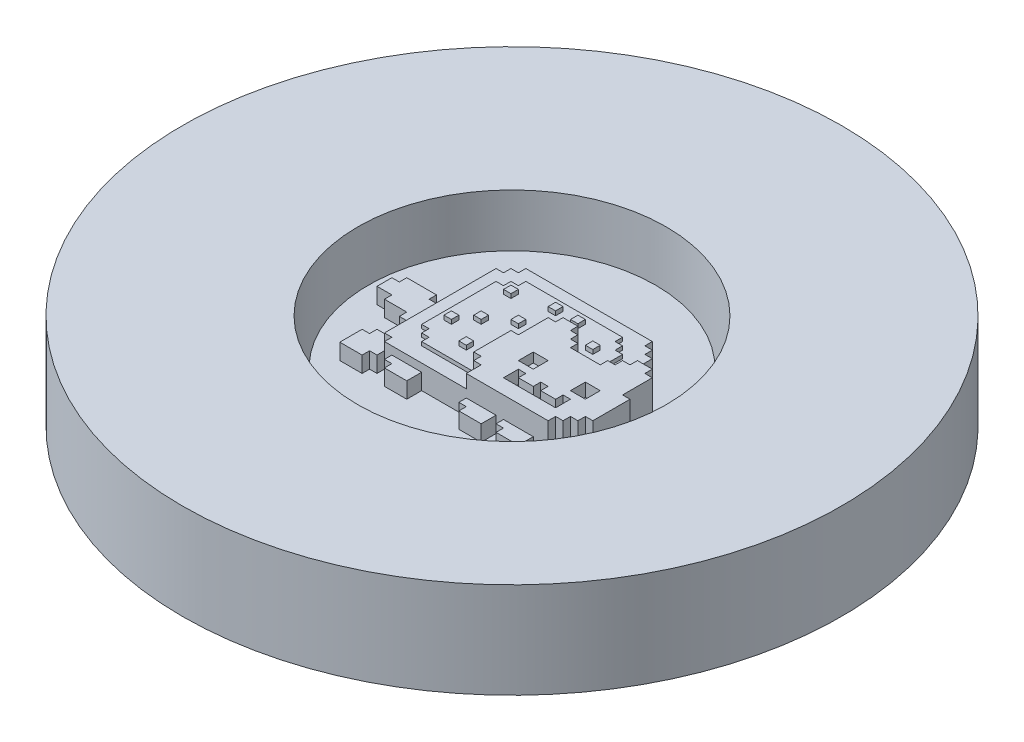
SolidWorks part; units mm, degrees
ref_plane "Front Plane" through (0, 0, 0) normal (0, 0, 1) x (1, 0, 0)
ref_plane "Top Plane" through (0, 0, 0) normal (0, 1, 0) x (1, 0, 0)
ref_plane "Right Plane" through (0, 0, 0) normal (1, 0, 0) x (0, 0, -1)
sketch "Sketch1"
sketch "face" plane through (0, 0, 0) normal (0, 1, 0) x (1, 0, 0)
  line L0 (103.124, 88.9) -> (110.236, 88.9)
  line L1 (110.236, 88.9) -> (110.236, 85.344)
  line L2 (110.236, 85.344) -> (113.792, 85.344)
  line L3 (113.792, 85.344) -> (113.792, 81.788)
  line L4 (113.792, 81.788) -> (117.348, 81.788)
  line L5 (117.348, 81.788) -> (117.348, 78.232)
  line L6 (117.348, 78.232) -> (131.572, 78.232)
  line L7 (131.572, 78.232) -> (131.572, 81.788)
  line L8 (131.572, 81.788) -> (135.128, 81.788)
  line L9 (135.128, 81.788) -> (135.128, 85.344)
  line L10 (135.128, 85.344) -> (138.684, 85.344)
  line L11 (138.684, 85.344) -> (138.684, 88.9)
  line L12 (138.684, 88.9) -> (145.796, 88.9)
  line L13 (145.796, 88.9) -> (145.796, 85.344)
  line L14 (145.796, 85.344) -> (149.352, 85.344)
  line L15 (149.352, 85.344) -> (149.352, 71.12)
  line L16 (149.352, 71.12) -> (152.908, 71.12)
  line L17 (152.908, 71.12) -> (152.908, 53.34)
  line L18 (152.908, 53.34) -> (149.352, 53.34)
  line L19 (149.352, 53.34) -> (149.352, 49.784)
  line L20 (149.352, 49.784) -> (145.796, 49.784)
  line L21 (145.796, 49.784) -> (145.796, 46.228)
  line L22 (145.796, 46.228) -> (142.24, 46.228)
  line L23 (142.24, 46.228) -> (142.24, 42.672)
  line L24 (142.24, 42.672) -> (103.124, 42.672)
  line L25 (103.124, 42.672) -> (103.124, 49.784)
  line L26 (103.124, 49.784) -> (99.568, 49.784)
  line L27 (99.568, 49.784) -> (99.568, 53.34)
  line L28 (99.568, 53.34) -> (96.012, 53.34)
  line L29 (96.012, 53.34) -> (96.012, 71.12)
  line L30 (96.012, 71.12) -> (99.568, 71.12)
  line L31 (99.568, 71.12) -> (99.568, 85.344)
  line L32 (99.568, 85.344) -> (103.124, 85.344)
  line L33 (110.236, 67.564) -> (110.236, 60.452)
  line L34 (110.236, 60.452) -> (117.348, 60.452)
  line L35 (117.348, 60.452) -> (117.348, 67.564)
  line L36 (117.348, 67.564) -> (110.236, 67.564)
  line L37 (135.128, 67.564) -> (135.128, 60.452)
  line L38 (135.128, 60.452) -> (142.24, 60.452)
  line L39 (142.24, 60.452) -> (142.24, 67.564)
  line L40 (142.24, 67.564) -> (135.128, 67.564)
  line L41 (113.792, 56.896) -> (113.792, 49.784)
  line L42 (113.792, 49.784) -> (138.684, 49.784)
  line L43 (138.684, 49.784) -> (138.684, 56.896)
  line L44 (138.684, 56.896) -> (135.128, 56.896)
  line L45 (135.128, 56.896) -> (135.128, 53.34)
  line L46 (135.128, 53.34) -> (128.016, 53.34)
  line L47 (128.016, 53.34) -> (128.016, 56.896)
  line L48 (128.016, 56.896) -> (124.46, 56.896)
  line L49 (124.46, 56.896) -> (124.46, 53.34)
  line L50 (124.46, 53.34) -> (117.348, 53.34)
  line L51 (117.348, 53.34) -> (117.348, 56.896)
  line L52 (117.348, 56.896) -> (113.792, 56.896)
  line L53 (103.124, 88.9) -> (103.124, 85.344)
sketch "poptart" plane through (0, 0, 0) normal (0, 1, 0) x (1, 0, 0)
  line L1 (135.128, 99.568) -> (131.572, 99.568)
  line L2 (131.572, 99.568) -> (131.572, 103.124)
  line L3 (131.572, 103.124) -> (128.016, 103.124)
  line L4 (128.016, 103.124) -> (128.016, 106.68)
  line L5 (128.016, 106.68) -> (67.564, 106.68)
  line L6 (67.564, 106.68) -> (67.564, 103.124)
  line L7 (67.564, 103.124) -> (64.008, 103.124)
  line L8 (64.008, 103.124) -> (64.008, 99.568)
  line L9 (64.008, 99.568) -> (60.452, 99.568)
  line L10 (60.452, 99.568) -> (60.452, 46.228)
  line L11 (60.452, 46.228) -> (64.008, 46.228)
  line L12 (64.008, 46.228) -> (64.008, 42.672)
  line L13 (64.008, 42.672) -> (135.128, 42.672)
  line L14 (142.24, 42.672) -> (103.124, 42.672) construction
  line L15 (135.128, 42.672) -> (145.796, 53.34)
  line L16 (145.796, 53.34) -> (145.796, 71.12)
  line L17 (145.796, 71.12) -> (135.128, 85.344)
  line L18 (135.128, 85.344) -> (135.128, 99.568)
sketch "feet tail" plane through (0, 0, 0) normal (0, 1, 0) x (1, 0, 0)
  line L0 (60.452, 74.676) -> (53.34, 74.676)
  line L1 (60.452, 99.568) -> (60.452, 46.228) construction
  line L2 (53.34, 74.676) -> (53.34, 78.232)
  line L3 (53.34, 78.232) -> (39.116, 78.232)
  line L4 (39.116, 78.232) -> (39.116, 74.676)
  line L5 (39.116, 74.676) -> (35.56, 74.676)
  line L6 (35.56, 74.676) -> (35.56, 67.564)
  line L7 (35.56, 67.564) -> (42.672, 67.564)
  line L8 (42.672, 67.564) -> (42.672, 64.008)
  line L9 (42.672, 64.008) -> (53.34, 64.008)
  line L10 (53.34, 64.008) -> (53.34, 60.452)
  line L11 (53.34, 60.452) -> (60.452, 60.452)
  line L12 (60.452, 60.452) -> (60.452, 74.676)
  line L13 (60.452, 53.34) -> (56.896, 53.34)
  line L14 (56.896, 53.34) -> (56.896, 49.784)
  line L15 (56.896, 49.784) -> (53.34, 49.784)
  line L16 (53.34, 49.784) -> (53.34, 46.228)
  line L17 (53.34, 46.228) -> (49.784, 46.228)
  line L18 (49.784, 46.228) -> (49.784, 35.56)
  line L19 (49.784, 35.56) -> (60.452, 35.56)
  line L20 (60.452, 35.56) -> (60.452, 39.116)
  line L21 (60.452, 39.116) -> (64.008, 39.116)
  line L22 (64.008, 39.116) -> (64.008, 46.228)
  line L23 (67.564, 42.672) -> (67.564, 39.116)
  line L24 (64.008, 42.672) -> (135.128, 42.672) construction
  line L25 (67.564, 39.116) -> (71.12, 39.116)
  line L26 (71.12, 39.116) -> (71.12, 35.56)
  line L27 (71.12, 35.56) -> (81.788, 35.56)
  line L28 (81.788, 35.56) -> (81.788, 42.672)
  line L29 (81.788, 42.672) -> (67.564, 42.672)
  line L30 (64.008, 46.228) -> (60.452, 46.228)
  line L31 (60.452, 46.228) -> (60.452, 53.34)
  line L33 (103.124, 42.672) -> (103.124, 39.116)
  line L34 (103.124, 39.116) -> (106.68, 39.116)
  line L35 (106.68, 39.116) -> (106.68, 35.56)
  line L36 (106.68, 35.56) -> (117.348, 35.56)
  line L37 (117.348, 35.56) -> (117.348, 42.672)
  line L38 (142.24, 42.672) -> (103.124, 42.672) construction
  line L39 (117.348, 42.672) -> (103.124, 42.672)
  line L40 (120.904, 42.672) -> (120.904, 39.116)
  line L41 (120.904, 39.116) -> (124.46, 39.116)
  line L42 (124.46, 39.116) -> (124.46, 35.56)
  line L43 (124.46, 35.56) -> (135.128, 35.56)
  line L44 (135.128, 35.56) -> (135.128, 42.672)
  line L45 (135.128, 42.672) -> (120.904, 42.672)
sketch "sprinkles" plane through (0, 0, 0) normal (0, 1, 0) x (1, 0, 0)
  line L1 (71.12, 67.564) -> (74.676, 67.564)
  line L2 (71.12, 67.564) -> (71.12, 64.008)
  line L3 (71.12, 64.008) -> (74.676, 64.008)
  line L4 (74.676, 67.564) -> (74.676, 64.008)
  line L5 (78.232, 74.676) -> (81.788, 74.676)
  line L6 (78.232, 74.676) -> (78.232, 71.12)
  line L7 (78.232, 71.12) -> (81.788, 71.12)
  line L8 (81.788, 74.676) -> (81.788, 71.12)
  line L9 (88.9, 81.788) -> (92.456, 81.788)
  line L10 (88.9, 81.788) -> (88.9, 78.232)
  line L11 (88.9, 78.232) -> (92.456, 78.232)
  line L12 (92.456, 81.788) -> (92.456, 78.232)
  line L13 (74.676, 92.456) -> (78.232, 92.456)
  line L14 (74.676, 92.456) -> (74.676, 88.9)
  line L15 (74.676, 88.9) -> (78.232, 88.9)
  line L16 (78.232, 92.456) -> (78.232, 88.9)
  line L17 (92.456, 96.012) -> (96.012, 96.012)
  line L18 (92.456, 96.012) -> (92.456, 92.456)
  line L19 (92.456, 92.456) -> (96.012, 92.456)
  line L20 (96.012, 96.012) -> (96.012, 92.456)
  line L21 (103.124, 96.012) -> (106.68, 96.012)
  line L22 (103.124, 96.012) -> (103.124, 92.456)
  line L23 (103.124, 92.456) -> (106.68, 92.456)
  line L24 (106.68, 96.012) -> (106.68, 92.456)
  line L25 (117.348, 88.9) -> (120.904, 88.9)
  line L26 (117.348, 88.9) -> (117.348, 85.344)
  line L27 (117.348, 85.344) -> (120.904, 85.344)
  line L28 (120.904, 88.9) -> (120.904, 85.344)
  line L29 (85.344, 60.452) -> (88.9, 60.452)
  line L30 (85.344, 60.452) -> (85.344, 56.896)
  line L31 (85.344, 56.896) -> (88.9, 56.896)
  line L32 (88.9, 60.452) -> (88.9, 56.896)
sketch "engrave poptart" plane through (0, 0, 0) normal (0, 1, 0) x (1, 0, 0)
  line L0 (71.12, 53.34) -> (74.676, 53.34)
  line L1 (74.676, 53.34) -> (74.676, 49.784)
  line L2 (74.676, 49.784) -> (99.8163, 49.76)
  line L3 (71.12, 53.34) -> (71.12, 56.896)
  line L4 (71.12, 56.896) -> (67.564, 56.896)
  line L5 (67.564, 56.896) -> (67.564, 92.456)
  line L6 (67.564, 92.456) -> (71.12, 92.456)
  line L7 (71.12, 92.456) -> (71.12, 96.012)
  line L8 (71.12, 96.012) -> (74.676, 96.012)
  line L9 (74.676, 96.012) -> (74.676, 99.568)
  line L10 (74.676, 99.568) -> (120.904, 99.568)
  line L11 (120.904, 99.568) -> (120.904, 96.012)
  line L12 (120.904, 96.012) -> (124.46, 96.012)
  line L13 (124.46, 96.012) -> (124.46, 92.456)
  line L14 (124.46, 92.456) -> (128.016, 92.456)
  line L15 (128.016, 92.456) -> (128.016, 67.564)
  line L16 (128.016, 67.564) -> (128.016, 64.008)
  line L17 (128.016, 64.008) -> (99.568, 49.784)
  line L18 (99.568, 49.784) -> (99.8163, 49.76)
sketch "rainbow tail" [suppressed] plane through (0, 0, 0) normal (0, 1, 0) x (1, 0, 0)
  line L0 (0, 39.116) -> (0, 49.784)
  line L1 (0, 49.784) -> (7.112, 49.784)
  line L2 (7.112, 49.784) -> (7.112, 53.34)
  line L3 (7.112, 53.34) -> (35.56, 53.34)
  line L4 (35.56, 53.34) -> (35.56, 49.784)
  line L5 (35.56, 49.784) -> (53.34, 49.784)
  line L6 (0, 39.116) -> (7.112, 39.116)
  line L7 (7.112, 39.116) -> (7.112, 42.672)
  line L8 (7.112, 42.672) -> (35.56, 42.672)
  line L9 (35.56, 42.672) -> (35.56, 39.116)
  line L10 (35.56, 39.116) -> (49.784, 39.116)
  line L11 (49.784, 46.228) -> (49.784, 35.56) construction
  line L12 (53.34, 49.784) -> (53.34, 46.228)
  line L13 (53.34, 46.228) -> (49.784, 46.228)
  line L14 (53.34, 60.452) -> (35.56, 60.452)
  line L15 (35.56, 60.452) -> (35.56, 64.008)
  line L16 (35.56, 64.008) -> (7.112, 64.008)
  line L17 (7.112, 64.008) -> (7.112, 60.452)
  line L18 (7.112, 60.452) -> (0, 60.452)
  line L19 (0, 60.452) -> (0, 71.12)
  line L20 (49.784, 46.228) -> (49.784, 39.116)
  line L21 (0, 71.12) -> (7.112, 71.12)
  line L22 (7.112, 71.12) -> (7.112, 74.676)
  line L23 (7.112, 74.676) -> (53.34, 74.676)
  line L24 (53.34, 74.676) -> (53.34, 60.452)
  line L25 (0, 81.788) -> (7.112, 81.788)
  line L26 (7.112, 81.788) -> (7.112, 85.344)
  line L27 (7.112, 85.344) -> (35.56, 85.344)
  line L28 (35.56, 85.344) -> (35.56, 81.788)
  line L29 (35.56, 81.788) -> (60.452, 81.788)
  line L30 (60.452, 81.788) -> (60.452, 92.456)
  line L31 (60.452, 92.456) -> (35.56, 92.456)
  line L32 (35.56, 92.456) -> (35.56, 96.012)
  line L33 (35.56, 96.012) -> (7.112, 96.012)
  line L34 (7.112, 96.012) -> (7.112, 92.456)
  line L35 (7.112, 92.456) -> (0, 92.456)
  line L36 (0, 92.456) -> (0, 81.788)
  circle A0 centre (0, 0) radius 68.1246
extrude "face-" add sketch "face" along normal blind 17.78
extrude "feettail" add sketch "feet tail" along normal blind 7.62
extrude "poptart-" add sketch "poptart" along normal blind 11.43
extrude "sprinkle" add sketch "sprinkles" along normal blind 15.24
extrude "engrave" add sketch "engrave poptart" along normal blind 13.208
sketch "Sketch2" plane through (0, 0, 0) normal (0, 1, 0) x (1, 0, 0)
  circle A0 centre (93.98, 73.66) radius 68.58
sketch "Sketch4" plane through (0, 0, 0) normal (0, 1, 0) x (1, 0, 0)
  circle A0 centre (93.98, 73.66) radius 157.48
  circle A1 centre (93.98, 73.66) radius 81.28 construction
  circle A2 centre (93.98, 73.66) radius 73.66
  dimension "D1" = 76.2
extrude "CUPCAKE" add sketch "Sketch2" against normal blind 15.24
extrude "retaining" add sketch "Sketch4" against normal blind 45.72 from offset 21.59
sketch "Sketch5" plane through (0, 0, 0) normal (0, 1, 0) x (1, 0, 0)
  circle A1 centre (93.98, 73.66) radius 81.28
extrude "cupcake body" add sketch "Sketch5" against normal blind 6.35 from offset 17.78 offset against normal yes
sketch "Sketch10" [suppressed] plane through (0, 0, 0) normal (0, 1, 0) x (1, 0, 0)
  line L0 (60.452, 92.456) -> (35.56, 92.456)
  line L1 (35.56, 92.456) -> (35.56, 96.012)
  line L2 (35.56, 96.012) -> (29.1448, 96.012)
  line L4 (26.4026, 85.344) -> (35.56, 85.344)
  line L5 (35.56, 85.344) -> (35.56, 81.788)
  line L6 (35.56, 81.788) -> (60.452, 81.788)
  line L7 (60.452, 81.788) -> (60.452, 92.456)
  line L8 (35.56, 74.676) -> (25.4075, 74.676)
  line L14 (26.0826, 64.008) -> (35.56, 64.008)
  line L15 (35.56, 64.008) -> (35.56, 60.452)
  line L16 (35.56, 60.452) -> (53.34, 60.452)
  line L17 (53.34, 60.452) -> (53.34, 64.008)
  line L18 (53.34, 64.008) -> (42.672, 64.008)
  line L19 (42.672, 64.008) -> (42.672, 67.564)
  line L20 (42.672, 67.564) -> (35.56, 67.564)
  line L21 (35.56, 74.676) -> (35.56, 67.564) construction
  line L22 (35.56, 67.564) -> (42.672, 67.564) construction
  line L23 (35.56, 67.564) -> (35.56, 74.676)
  line L24 (53.34, 49.784) -> (35.56, 49.784)
  line L25 (35.56, 49.784) -> (35.56, 53.34)
  line L26 (35.56, 53.34) -> (28.4795, 53.34)
  line L28 (32.8003, 42.672) -> (35.56, 42.672)
  line L29 (35.56, 42.672) -> (35.56, 39.116)
  line L30 (35.56, 39.116) -> (49.784, 39.116)
  line L31 (49.784, 39.116) -> (49.784, 46.228)
  line L32 (49.784, 46.228) -> (53.34, 46.228)
  line L33 (53.34, 46.228) -> (53.34, 49.784)
  arc A0 (29.1448, 96.012) -> (26.4026, 85.344) centre (93.98, 73.66) ccw
  arc A1 (28.4795, 53.34) -> (32.8003, 42.672) centre (93.98, 73.66) ccw
  arc A2 (25.4075, 74.676) -> (26.0826, 64.008) centre (93.98, 73.66) ccw
extrude "Boss-Extrude1" [suppressed] add sketch "Sketch10" along normal blind 2.54
sketch "Sketch11" [suppressed] plane through (0, 0, 0) normal (0, 1, 0) x (1, 0, 0)
  line L0 (26.0826, 64.008) -> (35.56, 64.008)
  line L1 (35.56, 64.008) -> (35.56, 60.452)
  line L2 (35.56, 60.452) -> (60.452, 60.452)
  line L3 (35.56, 60.452) -> (60.452, 60.452) construction
  line L4 (60.452, 60.452) -> (60.452, 53.34)
  line L5 (60.452, 53.34) -> (56.896, 53.34)
  line L6 (56.896, 53.34) -> (56.896, 49.784)
  line L7 (56.896, 53.34) -> (56.896, 49.784) construction
  line L8 (56.896, 53.34) -> (56.896, 49.784) construction
  line L9 (56.896, 49.784) -> (35.56, 49.784)
  line L10 (35.56, 49.784) -> (35.56, 53.34)
  line L11 (35.56, 53.34) -> (28.4795, 53.34)
  line L12 (60.452, 81.788) -> (60.452, 74.676)
  line L13 (60.452, 74.676) -> (53.34, 74.676)
  line L14 (53.34, 74.676) -> (53.34, 78.232)
  line L15 (53.34, 74.676) -> (53.34, 78.232) construction
  line L16 (53.34, 78.232) -> (39.116, 78.232) construction
  line L17 (53.34, 78.232) -> (39.116, 78.232)
  line L18 (39.116, 78.232) -> (39.116, 74.676)
  line L19 (7.112, 74.676) -> (53.34, 74.676) construction
  line L20 (39.116, 78.232) -> (39.116, 74.676) construction
  line L21 (39.116, 74.676) -> (25.4075, 74.676)
  line L22 (26.4026, 85.344) -> (35.56, 85.344)
  line L24 (35.56, 85.344) -> (35.56, 81.788)
  line L25 (35.56, 81.788) -> (60.452, 81.788)
  arc A0 (26.4026, 85.344) -> (25.4075, 74.676) centre (93.98, 73.66) ccw
  arc A1 (26.0826, 64.008) -> (28.4795, 53.34) centre (93.98, 73.66) ccw
extrude "Boss-Extrude2" [suppressed] add sketch "Sketch11" along normal blind 3.81
